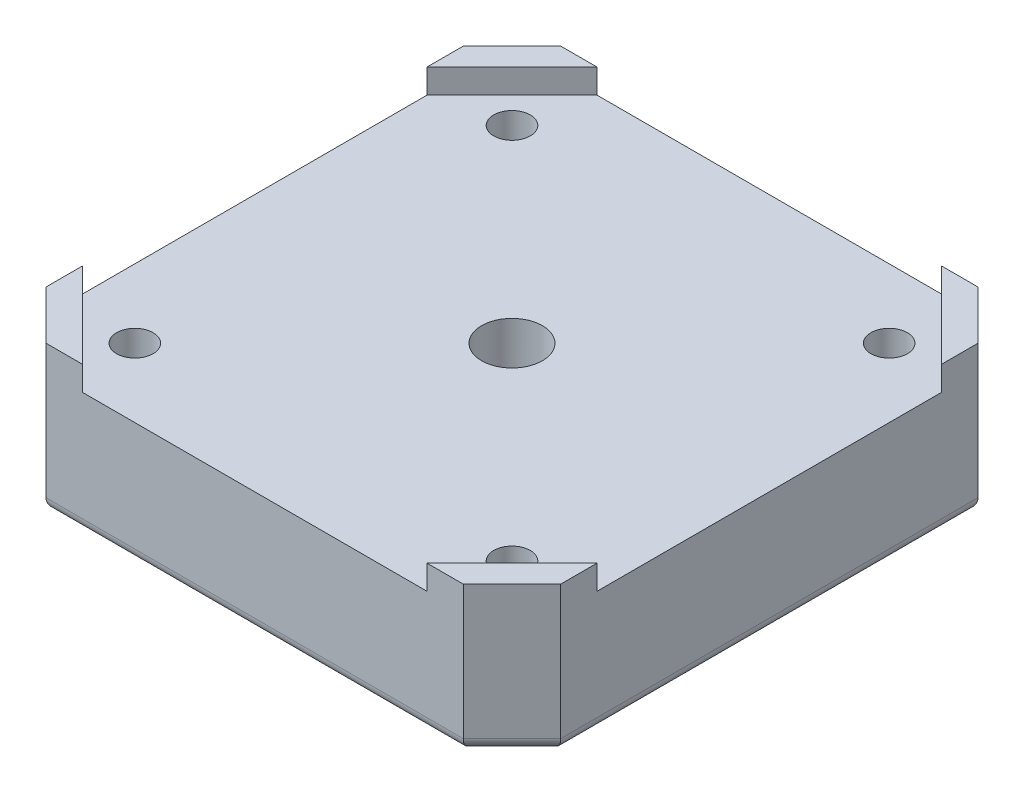
SolidWorks part; units mm, degrees
ref_plane "Front Plane" through (0, 0, 0) normal (0, 0, 1) x (1, 0, 0)
ref_plane "Top Plane" through (0, 0, 0) normal (0, 1, 0) x (1, 0, 0)
ref_plane "Right Plane" through (0, 0, 0) normal (1, 0, 0) x (0, 0, -1)
sketch "Sketch10" plane through (0, 0, 0) normal (0, 1, 0) x (1, 0, 0)
  line L0 (-21.15, 17.15) -> (-17.15, 21.15)
  line L1 (-17.15, -21.15) -> (17.15, -21.15)
  line L2 (-21.15, -17.15) -> (-21.15, 17.15)
  line L3 (-17.15, 21.15) -> (17.15, 21.15)
  line L4 (21.15, -17.15) -> (21.15, 17.15)
  line L5 (-21.15, -21.15) -> (21.15, 21.15) construction
  line L6 (-21.15, 21.15) -> (21.15, -21.15) construction
  line L7 (21.15, 17.15) -> (17.15, 21.15)
  line L8 (17.15, -21.15) -> (21.15, -17.15)
  line L9 (-21.15, -17.15) -> (-17.15, -21.15)
  point P0 (0, 0)
  dimension "D1" = 42.3
  dimension "D2" = 42.3
extrude "Boss-Extrude3" add sketch "Sketch10" along normal blind 12
sketch "Sketch11" plane through (0, 12, 0) normal (0, 1, 0) x (1, 0, 0)
  line L0 (21.15, -17.15) -> (21.15, 17.15) construction
  line L1 (-14.15, -21.15) -> (14.15, -21.15)
  line L2 (-21.15, -14.15) -> (-21.15, 14.15)
  line L3 (-14.15, 21.15) -> (14.15, 21.15)
  line L4 (21.15, -14.15) -> (21.15, 14.15)
  line L5 (-21.15, -21.15) -> (21.15, 21.15) construction
  line L6 (-21.15, 21.15) -> (21.15, -21.15) construction
  line L7 (17.15, 21.15) -> (-17.15, 21.15) construction
  line L8 (-21.15, 14.15) -> (-14.15, 21.15)
  line L9 (-21.15, -14.15) -> (-14.15, -21.15)
  line L10 (14.15, -21.15) -> (21.15, -14.15)
  line L11 (21.15, 14.15) -> (14.15, 21.15)
  point P0 (0, 0)
extrude "Cut-Extrude5" cut sketch "Sketch11" against normal blind 2
sketch "Sketch12" plane through (0, 10, 0) normal (0, 1, 0) x (1, 0, 0)
  circle A0 centre (0, 0) radius 2.5
  dimension "D1" = 5
extrude "Cut-Extrude6" cut sketch "Sketch12" against normal through all
sketch "Sketch13" plane through (0, 0, 0) normal (0, -1, 0) x (1, 0, 0)
  circle A0 centre (0, 0) radius 5.5
  dimension "D1" = 11
extrude "Cut-Extrude7" cut sketch "Sketch13" against normal blind 5
sketch "Sketch14" plane through (0, 0, 0) normal (0, -1, 0) x (1, 0, 0)
  line L1 (-15.5, -15.5) -> (15.5, -15.5) construction
  line L2 (-15.5, -15.5) -> (-15.5, 15.5) construction
  line L3 (-15.5, 15.5) -> (15.5, 15.5) construction
  line L4 (15.5, -15.5) -> (15.5, 15.5) construction
  line L5 (-15.5, -15.5) -> (15.5, 15.5) construction
  line L6 (-15.5, 15.5) -> (15.5, -15.5) construction
  circle A0 centre (-15.5, 15.5) radius 1.5
  circle A1 centre (15.5, 15.5) radius 1.5
  circle A2 centre (15.5, -15.5) radius 1.5
  circle A3 centre (-15.5, -15.5) radius 1.5
  circle A4 centre (0, 0) radius 2.5 construction
  circle A5 centre (0, 0) radius 5.5 construction
  point P0 (0, 0)
  point P16 (0, 0)
  dimension "D2" = 3
  dimension "D4" = 21.9203
  dimension "D5" = 15.5
  dimension "D1" = 31
  dimension "D3" = 4
extrude "Cut-Extrude8" cut sketch "Sketch14" against normal through all
sketch "Sketch15" plane through (0, 0, 0) normal (0, -1, 0) x (1, 0, 0)
  circle A0 centre (-15.5, 15.5) radius 3.1
  circle A1 centre (15.5, 15.5) radius 3.1
  circle A2 centre (15.5, -15.5) radius 3.1
  circle A3 centre (-15.5, -15.5) radius 3.1
  point P12 (0, 0)
  dimension "D1" = 6.2
  dimension "D2" = 4
extrude "Cut-Extrude9" cut sketch "Sketch15" against normal blind 2.6
fillet "Fillet1" radius 1 10 edges at (19.15, 0, -19.15) (0, 0, -21.15) (-19.15, 0, -19.15) (-21.15, 0, 0) (-19.15, 0, 19.15) (0, 0, 21.15) (19.15, 0, 19.15) (21.15, 0, 0) (0, 5, -5.5) (0, 0, -5.5)
fillet "Fillet2" radius 0.5 4 edges at (-15.5, 0, 12.4) (15.5, 0, 12.4) (15.5, 0, -18.6) (-15.5, 0, -18.6)
